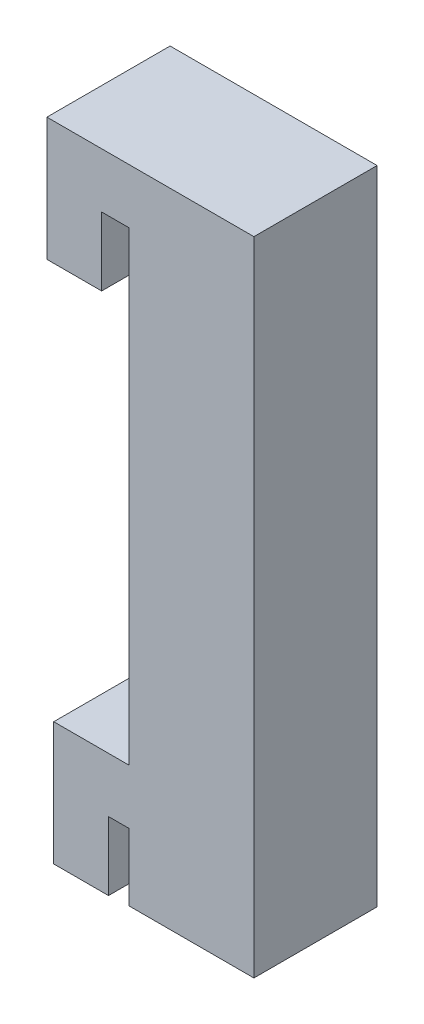
SolidWorks part; units mm, degrees
ref_plane "Plan de face" through (0, 0, 0) normal (0, 0, 1) x (1, 0, 0)
ref_plane "Plan de dessus" through (0, 0, 0) normal (0, 1, 0) x (1, 0, 0)
ref_plane "Plan de droite" through (0, 0, 0) normal (1, 0, 0) x (0, 0, -1)
sketch "Esquisse1" plane through (0, 0, 0) normal (0, 0, 1) x (1, 0, 0)
  line L0 (0, 0) -> (0, 5)
  line L1 (0, 5) -> (1.5, 5)
  line L4 (1.5, 0.0964) -> (10.6219, 0.0964)
  line L5 (10.6219, 0.0964) -> (10.6219, 47)
  line L8 (10.6219, 47) -> (-4.5, 47)
  line L9 (1.5, 43) -> (-0.5, 43)
  line L10 (0, 0) -> (-4, 0)
  line L11 (-4, 0) -> (-4, 9)
  line L12 (-4, 9) -> (1.5, 9)
  line L13 (1.5, 9) -> (1.5, 43)
  line L14 (-0.5, 43) -> (-0.5, 38)
  line L15 (-0.5, 38) -> (-4.5, 38)
  line L16 (-4.5, 38) -> (-4.5, 47)
  line L17 (1.5, 5) -> (1.5, 0.0964)
  point P11 (0.75, 5)
  dimension "D1" = 38
  dimension "D2" = 1.5
  dimension "D3" = 2
  dimension "D4" = 9
  dimension "D5" = 9
  dimension "D6" = 4
  dimension "D7" = 4
  dimension "D8" = 4
  dimension "D9" = 4
extrude "Boss.-Extru.1" add sketch "Esquisse1" along normal blind 9
